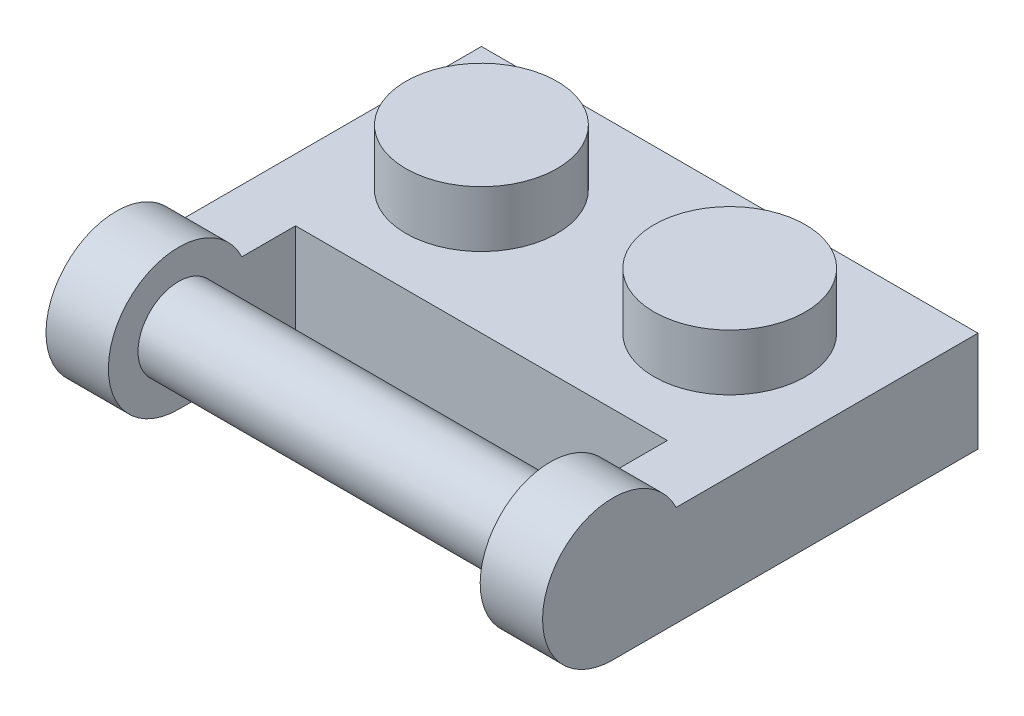
SolidWorks part; units mm, degrees
material "Grey"
ref_plane "Front Plane" through (0, 0, 0) normal (0, 0, 1) x (1, 0, 0)
ref_plane "Top Plane" through (0, 0, 0) normal (0, 1, 0) x (1, 0, 0)
ref_plane "Right Plane" through (0, 0, 0) normal (1, 0, 0) x (0, 0, -1)
sketch "Sketch1" plane through (0, 0, 0) normal (0, 1, 0) x (1, 0, 0)
  line L1 (-3.98, 3.98) -> (3.98, 3.98)
  line L2 (-3.98, 3.98) -> (-3.98, -3.98)
  line L3 (-3.98, -3.98) -> (3.98, -3.98)
  line L4 (3.98, 3.98) -> (3.98, -3.98)
  line L5 (-3.98, 3.98) -> (3.98, -3.98) construction
  line L6 (-3.98, -3.98) -> (3.98, 3.98) construction
  point P0 (0, 0)
  dimension "D1" = 7.96
extrude "Extrude1" add sketch "Sketch1" along normal blind 3.22
sketch "Sketch2" plane through (0, 3.22, 0) normal (0, 1, 0) x (1, 0, 0)
  circle A0 centre (0, 0) radius 2.425
  dimension "D1" = 4.85
extrude "Extrude2" add sketch "Sketch2" along normal blind 1.8
pattern_linear "LPattern1" count 2 spacing 7.96 along (1, 0, 0) of "Extrude2", "Extrude1"
shell "Shell1" thickness 1.55
sketch "Sketch4" plane through (0, 1.67, 0) normal (0, -1, 0) x (1, 0, 0)
  line L0 (10.39, 2.43) -> (10.39, -2.43) construction
  line L1 (-2.43, 2.43) -> (10.39, 2.43) construction
  line L2 (-2.43, -2.43) -> (-2.43, 2.43) construction
  line L3 (10.39, -2.43) -> (-2.43, -2.43) construction
  line L4 (10.39, 2.43) -> (10.39, -2.43)
  line L5 (-2.43, 2.43) -> (10.39, 2.43)
  line L6 (-2.43, -2.43) -> (-2.43, 2.43)
  line L7 (10.39, -2.43) -> (-2.43, -2.43)
extrude "Extrude3" cut sketch "Sketch4" against normal blind 0.14
sketch "Sketch5" plane through (0, 1.81, 0) normal (0, -1, 0) x (1, 0, 0)
  line L0 (10.39, 2.43) -> (-2.43, 2.43) construction
  circle A0 centre (3.98, 0) radius 1.5
  circle A1 centre (3.98, 0) radius 0.64
  point P5 (3.98, 2.43)
  dimension "D1" = 3
  dimension "D2" = 0.86
extrude "Extrude4" add sketch "Sketch5" along normal up to surface (1.81 mm away) up to face at (3.98, 0, 0)
sketch "Sketch6" plane through (11.94, 0, 0) normal (1, 0, 0) x (0, 0, -1)
  line L0 (-3.98, 0) -> (-5.7457, 0) construction
  line L1 (-7.73, 0) -> (-3.98, 0)
  line L2 (-3.98, 3.22) -> (-3.98, 0) construction
  line L3 (-3.98, 3.22) -> (-5.6998, 3.22)
  line L5 (-3.98, 0) -> (3.98, 0) construction
  line L7 (-3.98, 3.22) -> (-4.8911, 3.22) construction
  line L8 (-3.98, 3.22) -> (-3.98, 0)
  arc A0 (-4.8911, 3.22) -> (-7.73, 5.25) centre (-7.73, 2.25) ccw construction
  arc A1 (-7.73, 0.95) -> (-7.73, 3.55) centre (-7.73, 2.25) ccw construction
  arc A2 (-7.73, -0.75) -> (-5.7457, 0) centre (-7.73, 2.25) ccw construction
  arc A3 (-7.73, 0.95) -> (-7.73, -0.75) centre (-7.73, 0.1) ccw construction
  arc A4 (-7.73, 5.25) -> (-7.73, 3.55) centre (-7.73, 4.4) ccw construction
  arc A5 (-5.6998, 3.22) -> (-7.73, 0) centre (-7.73, 2.25) ccw
  dimension "D1" = 6
  dimension "D2" = 1.7
  dimension "D3" = 3.75
  dimension "D5" = 1.3
  dimension "D4" = 2.25
extrude "Extrude5" add sketch "Sketch6" against normal blind 2
sketch "Sketch7" plane through (-3.98, 0, 0) normal (-1, 0, 0) x (0, 0, 1)
  line L0 (3.98, 3.22) -> (3.98, 0) construction
  line L1 (3.98, 3.22) -> (5.6998, 3.22) construction
  line L2 (7.73, 0) -> (3.98, 0) construction
  line L3 (3.98, 3.22) -> (3.98, 0)
  line L4 (3.98, 3.22) -> (5.6998, 3.22)
  line L5 (7.73, 0) -> (3.98, 0)
  arc A0 (7.73, 0) -> (5.6998, 3.22) centre (7.73, 2.25) ccw construction
  arc A1 (7.73, 0) -> (5.6998, 3.22) centre (7.73, 2.25) ccw
extrude "Extrude6" add sketch "Sketch7" against normal blind 2
sketch "Sketch8" plane through (-3.98, 0, 0) normal (-1, 0, 0) x (0, 0, 1)
  circle A0 centre (7.73, 2.25) radius 1.3
  dimension "D1" = 2.6
extrude "Extrude7" add sketch "Sketch8" against normal up to surface (15.92 mm away) up to face at (11.94, 2.07, 2.0971)
